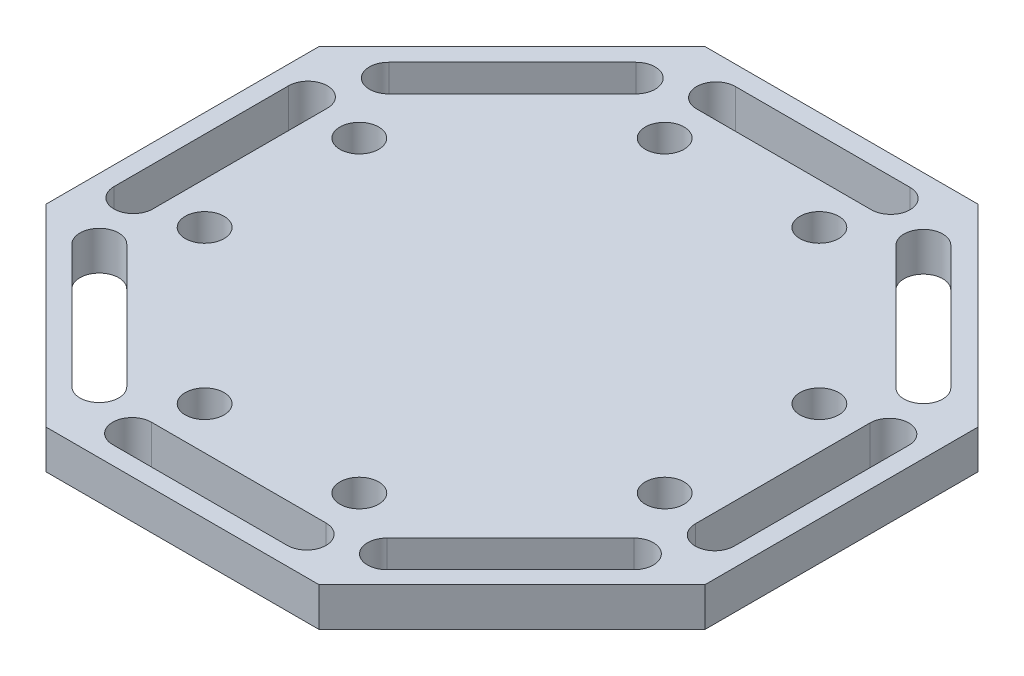
SolidWorks part; units mm, degrees
ref_plane "Front Plane" through (0, 0, 0) normal (0, 0, 1) x (1, 0, 0)
ref_plane "Top Plane" through (0, 0, 0) normal (0, 1, 0) x (1, 0, 0)
ref_plane "Right Plane" through (0, 0, 0) normal (1, 0, 0) x (0, 0, -1)
sketch "Sketch1" plane through (0, 0, 0) normal (0, 1, 0) x (1, 0, 0)
  line L0 (-25.47, 10.55) -> (25.47, 10.55) construction
  line L5 (10.55, -25.47) -> (25.47, -10.55)
  line L6 (25.47, -10.55) -> (25.47, 10.55)
  line L11 (25.47, 10.55) -> (10.55, 25.47)
  line L12 (10.55, 25.47) -> (-10.55, 25.47)
  line L13 (-10.55, 25.47) -> (-25.47, 10.55)
  line L14 (-25.47, 10.55) -> (-25.47, -10.55)
  line L15 (-25.47, -10.55) -> (-10.55, -25.47)
  line L16 (-10.55, -25.47) -> (10.55, -25.47)
  line L17 (-25.47, -10.55) -> (25.47, -10.55) construction
  line L18 (10.55, -25.47) -> (10.55, 25.47) construction
  line L19 (-10.55, -25.47) -> (-10.55, 25.47) construction
  line L20 (-6.7, 22.47) -> (6.8, 22.47) construction
  line L21 (-6.7, 23.97) -> (6.8, 23.97)
  line L22 (-6.7, 20.97) -> (6.8, 20.97)
  line L23 (10.1257, 19.551) -> (19.6717, 10.005)
  line L24 (12.2471, 21.6723) -> (21.793, 12.1263)
  line L25 (11.1864, 20.6116) -> (20.7323, 11.0657) construction
  line L26 (21.02, 6.65) -> (21.02, -6.85)
  line L27 (24.02, 6.65) -> (24.02, -6.85)
  line L28 (22.52, 6.65) -> (22.52, -6.85) construction
  line L29 (19.601, -10.1757) -> (10.055, -19.7217)
  line L30 (21.7223, -12.2971) -> (12.1763, -21.843)
  line L31 (20.6616, -11.2364) -> (11.1157, -20.7823) construction
  line L32 (6.7, -21.07) -> (-6.8, -21.07)
  line L33 (6.7, -24.07) -> (-6.8, -24.07)
  line L34 (6.7, -22.57) -> (-6.8, -22.57) construction
  line L35 (-10.1257, -19.651) -> (-19.6717, -10.105)
  line L36 (-12.2471, -21.7723) -> (-21.793, -12.2263)
  line L37 (-11.1864, -20.7116) -> (-20.7323, -11.1657) construction
  line L38 (-21.02, -6.75) -> (-21.02, 6.75)
  line L39 (-24.02, -6.75) -> (-24.02, 6.75)
  line L40 (-22.52, -6.75) -> (-22.52, 6.75) construction
  line L41 (-19.601, 10.0757) -> (-10.055, 19.6217)
  line L42 (-21.7223, 12.1971) -> (-12.1763, 21.743)
  line L43 (-20.6616, 11.1364) -> (-11.1157, 20.6823) construction
  circle A8 centre (0, 0) radius 25.47 construction
  circle A9 centre (-17.78, 5.978) radius 1.5
  circle A10 centre (-17.78, -5.978) radius 1.5
  circle A11 centre (5.978, 17.78) radius 1.5
  circle A12 centre (-5.978, 17.78) radius 1.5
  circle A13 centre (17.78, -5.978) radius 1.5
  circle A14 centre (17.78, 5.978) radius 1.5
  circle A15 centre (-5.978, -17.78) radius 1.5
  circle A16 centre (5.978, -17.78) radius 1.5
  arc A17 (-6.7, 23.97) -> (-6.7, 20.97) centre (-6.7, 22.47) ccw
  arc A18 (6.8, 20.97) -> (6.8, 23.97) centre (6.8, 22.47) ccw
  arc A19 (12.2471, 21.6723) -> (10.1257, 19.551) centre (11.1864, 20.6116) ccw
  arc A20 (19.6717, 10.005) -> (21.793, 12.1263) centre (20.7323, 11.0657) ccw
  arc A21 (24.02, 6.65) -> (21.02, 6.65) centre (22.52, 6.65) ccw
  arc A22 (21.02, -6.85) -> (24.02, -6.85) centre (22.52, -6.85) ccw
  arc A23 (21.7223, -12.2971) -> (19.601, -10.1757) centre (20.6616, -11.2364) ccw
  arc A24 (10.055, -19.7217) -> (12.1763, -21.843) centre (11.1157, -20.7823) ccw
  arc A25 (6.7, -24.07) -> (6.7, -21.07) centre (6.7, -22.57) ccw
  arc A26 (-6.8, -21.07) -> (-6.8, -24.07) centre (-6.8, -22.57) ccw
  arc A27 (-12.2471, -21.7723) -> (-10.1257, -19.651) centre (-11.1864, -20.7116) ccw
  arc A28 (-19.6717, -10.105) -> (-21.793, -12.2263) centre (-20.7323, -11.1657) ccw
  arc A29 (-24.02, -6.75) -> (-21.02, -6.75) centre (-22.52, -6.75) ccw
  arc A30 (-21.02, 6.75) -> (-24.02, 6.75) centre (-22.52, 6.75) ccw
  arc A31 (-21.7223, 12.1971) -> (-19.601, 10.0757) centre (-20.6616, 11.1364) ccw
  arc A32 (-10.055, 19.6217) -> (-12.1763, 21.743) centre (-11.1157, 20.6823) ccw
  point P5 (0, 0)
  point P15 (0.05, 22.47)
  point P30 (0, 0)
  point P35 (0, 0)
  point P36 (0, 0)
  point P37 (0, 0)
  point P38 (15.9594, 15.8387)
  point P45 (22.52, -0.1)
  point P53 (15.8887, -16.0094)
  point P60 (-0.05, -22.57)
  point P67 (-15.9594, -15.9387)
  point P74 (-22.52, 0)
  point P81 (-15.8887, 15.9094)
  point P88 (0, -0.05)
  point P89 (0, 0)
  dimension "D3" = 4.572
  dimension "D2" = 3
  dimension "D9" = 1.5
  dimension "D1" = 21.1
  dimension "D4" = 17.78
  dimension "D5" = 4.572
  dimension "D6" = 13.5
  dimension "D7" = 3.75
  dimension "D8" = 3
extrude "Boss-Extrude1" add sketch "Sketch1" along normal blind 3
